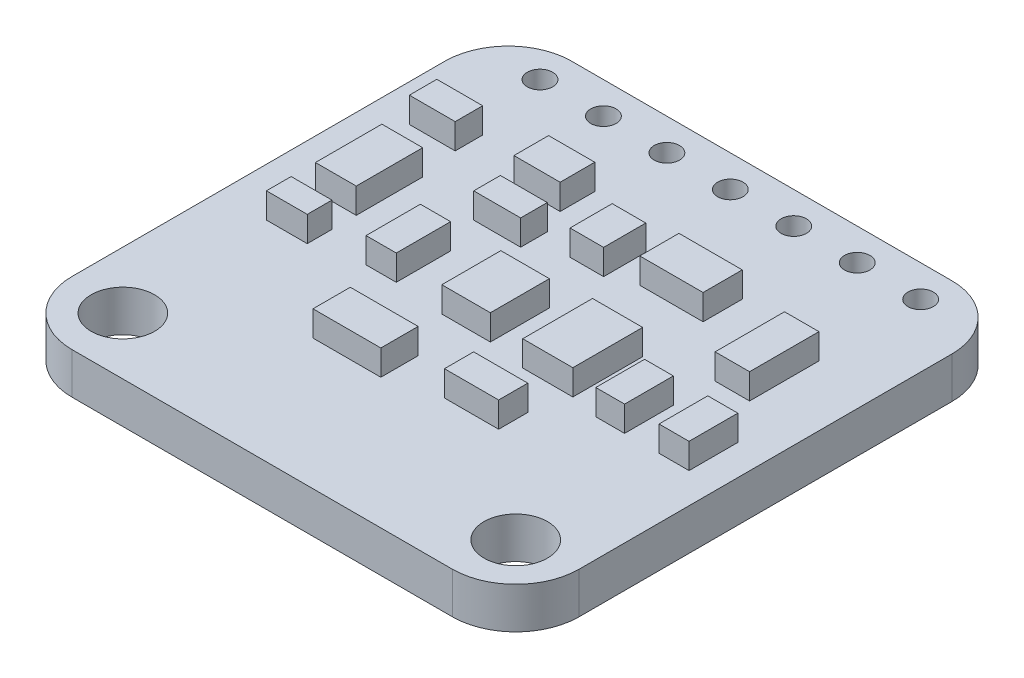
SolidWorks part; units mm, degrees
material "Melamine resin"
ref_plane "Front Plane" through (0, 0, 0) normal (0, 0, 1) x (1, 0, 0)
ref_plane "Top Plane" through (0, 0, 0) normal (0, 1, 0) x (1, 0, 0)
ref_plane "Right Plane" through (0, 0, 0) normal (1, 0, 0) x (0, 0, -1)
sketch "Sketch1" plane through (0, 0, 0) normal (0, 1, 0) x (1, 0, 0)
  line L1 (-7.61, -10) -> (7.61, -10)
  line L2 (-10.15, -7.46) -> (-10.15, 7.46)
  line L3 (-7.61, 10) -> (7.61, 10)
  line L4 (10.15, -7.46) -> (10.15, 7.46)
  line L5 (-10.15, -10) -> (10.15, 10) construction
  line L6 (-10.15, 10) -> (10.15, -10) construction
  arc A0 (7.61, 10) -> (10.15, 7.46) centre (7.61, 7.46) cw
  arc A1 (-10.15, 7.46) -> (-7.61, 10) centre (-7.61, 7.46) cw
  arc A2 (-7.61, -10) -> (-10.15, -7.46) centre (-7.61, -7.46) cw
  arc A3 (7.61, -10) -> (10.15, -7.46) centre (7.61, -7.46) ccw
  point P0 (0, 0)
  dimension "D3" = 2.54
  dimension "D1" = 20.3
  dimension "D2" = 20
extrude "pcb" add sketch "Sketch1" along normal blind 1.651
sketch "Sketch2" plane through (0, 0, 0) normal (0, -1, 0) x (1, 0, 0)
  line L0 (-7.864, 7.714) -> (11.3977, 7.714) construction
  line L1 (-7.61, 10) -> (7.61, 10) construction
  line L2 (-10.15, -7.46) -> (-10.15, 7.46) construction
  line L3 (10.15, 7.46) -> (10.15, -7.46) construction
  line L4 (-7.61, -8.73) -> (7.2534, -8.73) construction
  line L5 (7.61, -10) -> (-7.61, -10) construction
  line L6 (-10.15, -7.46) -> (-10.15, 7.46) construction
  circle A0 centre (-7.864, 7.714) radius 1.27
  circle A1 centre (7.864, 7.714) radius 1.27
  circle A2 centre (-7.61, -8.73) radius 0.508
  circle A3 centre (-5.07, -8.73) radius 0.508
  circle A4 centre (-2.53, -8.73) radius 0.508
  circle A5 centre (0.01, -8.73) radius 0.508
  circle A6 centre (2.55, -8.73) radius 0.508
  circle A7 centre (5.09, -8.73) radius 0.508
  circle A8 centre (7.63, -8.73) radius 0.508
  dimension "D1" = 2.54
  dimension "D5" = 1.016
  dimension "D2" = 2.286
  dimension "D3" = 2.286
  dimension "D4" = 2.286
  dimension "D7" = 1.27
  dimension "D8" = 2.54
  dimension "D6" = 7
extrude "Cut-Extrude1" cut sketch "Sketch2" against normal through all
sketch "Sketch3" plane through (0, 1.651, 0) normal (0, 1, 0) x (1, 0, 0)
  line L0 (-7.61, -10) -> (7.61, -10) construction
  line L1 (0.498, -1.364) -> (-1.4451, -1.364)
  line L2 (0.498, -1.364) -> (0.498, 0.9982)
  line L3 (0.498, 0.9982) -> (-1.4451, 0.9982)
  line L4 (-1.4451, -1.364) -> (-1.4451, 0.9982)
  line L5 (0.498, -1.364) -> (-1.4451, 0.9982) construction
  line L6 (0.498, 0.9982) -> (-1.4451, -1.364) construction
  line L7 (10.15, -7.46) -> (10.15, 7.46) construction
  line L61 (4.054, -1.618) -> (2.0474, -1.618)
  line L62 (4.054, -1.618) -> (4.054, 1.176)
  line L63 (4.054, 1.176) -> (2.0474, 1.176)
  line L64 (2.0474, -1.618) -> (2.0474, 1.176)
  line L66 (3.6875, -4.223) -> (1.5193, -4.223)
  line L67 (3.6875, -4.223) -> (3.6875, -3.0552)
  line L68 (3.6875, -3.0552) -> (1.5193, -3.0552)
  line L69 (1.5193, -4.223) -> (1.5193, -3.0552)
  line L70 (-0.4735, -4.7775) -> (-3.1897, -4.7775)
  line L71 (-0.4735, -4.7775) -> (-0.4735, -3.284)
  line L72 (-0.4735, -3.284) -> (-3.1897, -3.284)
  line L73 (-3.1897, -4.7775) -> (-3.1897, -3.284)
  line L74 (-3.4564, -1.1769) -> (-4.666, -1.1769)
  line L75 (-3.4564, -1.1769) -> (-3.4564, 0.9982)
  line L76 (-3.4564, 0.9982) -> (-4.666, 0.9982)
  line L77 (-4.666, -1.1769) -> (-4.666, 0.9982)
  line L78 (-6.5788, 0.3435) -> (-8.2121, 0.3435)
  line L79 (-6.5788, 0.3435) -> (-6.5788, 3.0034)
  line L80 (-6.5788, 3.0034) -> (-8.2121, 3.0034)
  line L81 (-8.2121, 0.3435) -> (-8.2121, 3.0034)
  line L82 (-6.8328, 4.5581) -> (-8.6672, 4.5581)
  line L83 (-6.8328, 4.5581) -> (-6.8328, 5.6583)
  line L84 (-6.8328, 5.6583) -> (-8.6672, 5.6583)
  line L85 (-8.6672, 4.5581) -> (-8.6672, 5.6583)
  line L86 (-2.631, 4.5581) -> (-4.4793, 4.5581)
  line L87 (-2.631, 4.5581) -> (-2.631, 5.9441)
  line L88 (-2.631, 5.9441) -> (-4.4793, 5.9441)
  line L89 (-4.4793, 4.5581) -> (-4.4793, 5.9441)
  line L90 (-2.1838, 2.5294) -> (-4.0612, 2.5294)
  line L91 (-2.1838, 2.5294) -> (-2.1838, 3.5957)
  line L92 (-2.1838, 3.5957) -> (-4.0612, 3.5957)
  line L93 (-4.0612, 2.5294) -> (-4.0612, 3.5957)
  line L94 (-6.5788, -1.618) -> (-8.2121, -1.618)
  line L95 (-6.5788, -1.618) -> (-6.5788, -0.6294)
  line L96 (-6.5788, -0.6294) -> (-8.2121, -0.6294)
  line L97 (-8.2121, -1.618) -> (-8.2121, -0.6294)
  line L98 (6.3518, -1.8447) -> (5.1989, -1.8447)
  line L99 (6.3518, -1.8447) -> (6.3518, 0.108)
  line L100 (6.3518, 0.108) -> (5.1989, 0.108)
  line L101 (5.1989, -1.8447) -> (5.1989, 0.108)
  line L102 (8.9319, -1.8447) -> (7.7303, -1.8447)
  line L103 (8.9319, -1.8447) -> (8.9319, 0.108)
  line L104 (8.9319, 0.108) -> (7.7303, 0.108)
  line L105 (7.7303, -1.8447) -> (7.7303, 0.108)
  line L106 (7.7303, 1.78) -> (6.3518, 1.78)
  line L107 (7.7303, 1.78) -> (7.7303, 4.5581)
  line L108 (7.7303, 4.5581) -> (6.3518, 4.5581)
  line L109 (6.3518, 1.78) -> (6.3518, 4.5581)
  line L110 (1.5193, 3.5957) -> (4.054, 3.5957)
  line L111 (1.5193, 3.5957) -> (1.5193, 5.1642)
  line L112 (1.5193, 5.1642) -> (4.054, 5.1642)
  line L113 (4.054, 3.5957) -> (4.054, 5.1642)
  line L114 (0.498, 3.1691) -> (-0.8461, 3.1691)
  line L115 (0.498, 3.1691) -> (0.498, 4.8573)
  line L116 (0.498, 4.8573) -> (-0.8461, 4.8573)
  line L117 (-0.8461, 3.1691) -> (-0.8461, 4.8573)
  point P0 (-0.4735, -0.1829)
  dimension "D1" = 1.9431
  dimension "D2" = 2.3622
  dimension "D3" = 8.636
  dimension "D4" = 9.652
  dimension "D5" = 2.0066
  dimension "D6" = 2.794
  dimension "D7" = 6.096
  dimension "D8" = 8.382
extrude "components" add sketch "Sketch3" along normal blind 1.016
